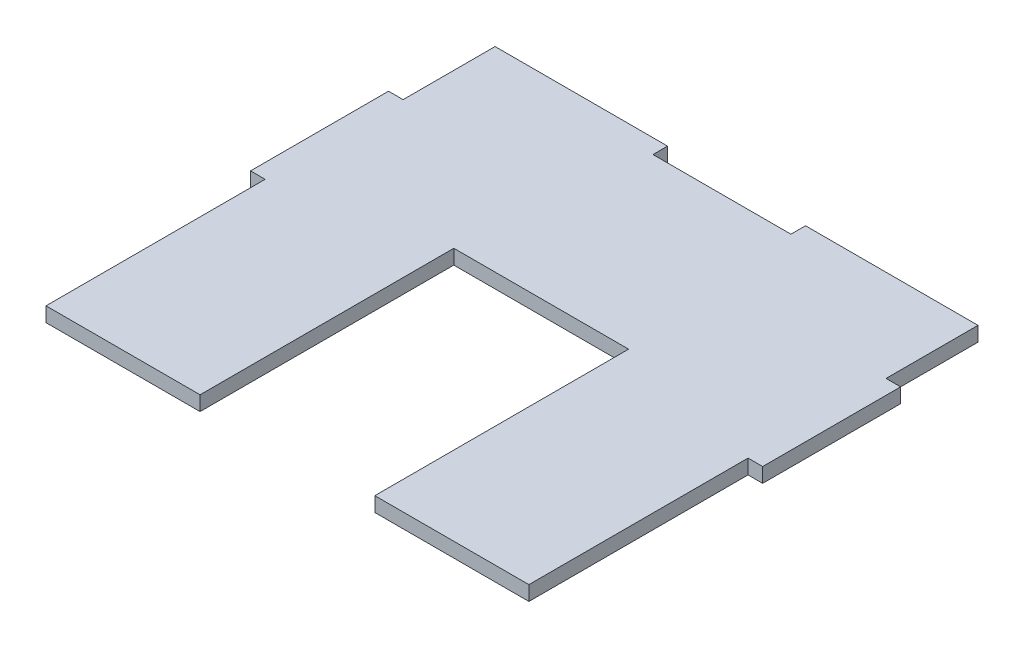
SolidWorks part; units mm, degrees
ref_plane "Front Plane" through (0, 0, 0) normal (0, 0, 1) x (1, 0, 0)
ref_plane "Top Plane" through (0, 0, 0) normal (0, 1, 0) x (1, 0, 0)
ref_plane "Right Plane" through (0, 0, 0) normal (1, 0, 0) x (0, 0, -1)
sketch "Sketch1" plane through (0, 0, 0) normal (0, 1, 0) x (1, 0, 0)
  line L0 (33.5, 52) -> (33.5, 0)
  line L1 (0, 0) -> (105, 0)
  line L2 (0, 0) -> (0, 94.475)
  line L3 (0, 94.475) -> (105, 94.475)
  line L4 (105, 0) -> (105, 94.475)
  line L5 (33.5, 52) -> (71.5, 52)
  line L6 (33.5, 0) -> (71.5, 0)
  line L7 (71.5, 52) -> (71.5, 0)
  line L8 (33.5, 52) -> (71.5, 0) construction
  line L9 (33.5, 0) -> (71.5, 52) construction
  line L10 (37.5, 91.3) -> (37.5, 94.475)
  line L11 (37.5, 91.3) -> (67.5, 91.3)
  line L12 (37.5, 94.475) -> (67.5, 94.475)
  line L13 (67.5, 91.3) -> (67.5, 94.475)
  line L14 (37.5, 91.3) -> (67.5, 94.475) construction
  line L15 (37.5, 94.475) -> (67.5, 91.3) construction
  line L17 (0, 0) -> (33.5, 0)
  line L18 (0, 0) -> (0, -3.175)
  line L19 (0, -3.175) -> (33.5, -3.175)
  line L20 (33.5, 0) -> (33.5, -3.175)
  line L21 (71.5, 0) -> (105, 0)
  line L22 (71.5, 0) -> (71.5, -3.175)
  line L23 (71.5, -3.175) -> (105, -3.175)
  line L24 (105, 0) -> (105, -3.175)
  line L25 (-3.175, 74.475) -> (0, 74.475)
  line L26 (-3.175, 74.475) -> (-3.175, 44.475)
  line L27 (-3.175, 44.475) -> (0, 44.475)
  line L28 (0, 74.475) -> (0, 44.475)
  line L29 (-3.175, 74.475) -> (0, 44.475) construction
  line L30 (-3.175, 44.475) -> (0, 74.475) construction
  line L31 (108.175, 74.475) -> (105, 74.475)
  line L32 (108.175, 74.475) -> (108.175, 44.475)
  line L33 (108.175, 44.475) -> (105, 44.475)
  line L34 (105, 74.475) -> (105, 44.475)
  line L35 (108.175, 74.475) -> (105, 44.475) construction
  line L36 (108.175, 44.475) -> (105, 74.475) construction
  point P6 (52.5, 26)
  point P7 (52.5, 0)
  point P8 (52.5, 92.8875)
  point P13 (52.5, 94.475)
  point P21 (-1.5875, 59.475)
  point P26 (106.5875, 59.475)
  point P31 (0, 0)
  point P32 (0, 0)
  dimension "D1" = 105
  dimension "D2" = 94.475
  dimension "D3" = 38
  dimension "D4" = 52
  dimension "D5" = 3.175
  dimension "D6" = 30
  dimension "D7" = 3.175
  dimension "D8" = 3.175
  dimension "D9" = 20
  dimension "D10" = 30
extrude "Boss-Extrude1" add sketch "Sketch1" along normal blind 3.175 contours L5 L7 L1 L4 L3 L2 L0 | L20 L1 L18 L19 | L24 L1 L22 L23 | L26 L27 L2 L25 | L33 L32 L31 L4
